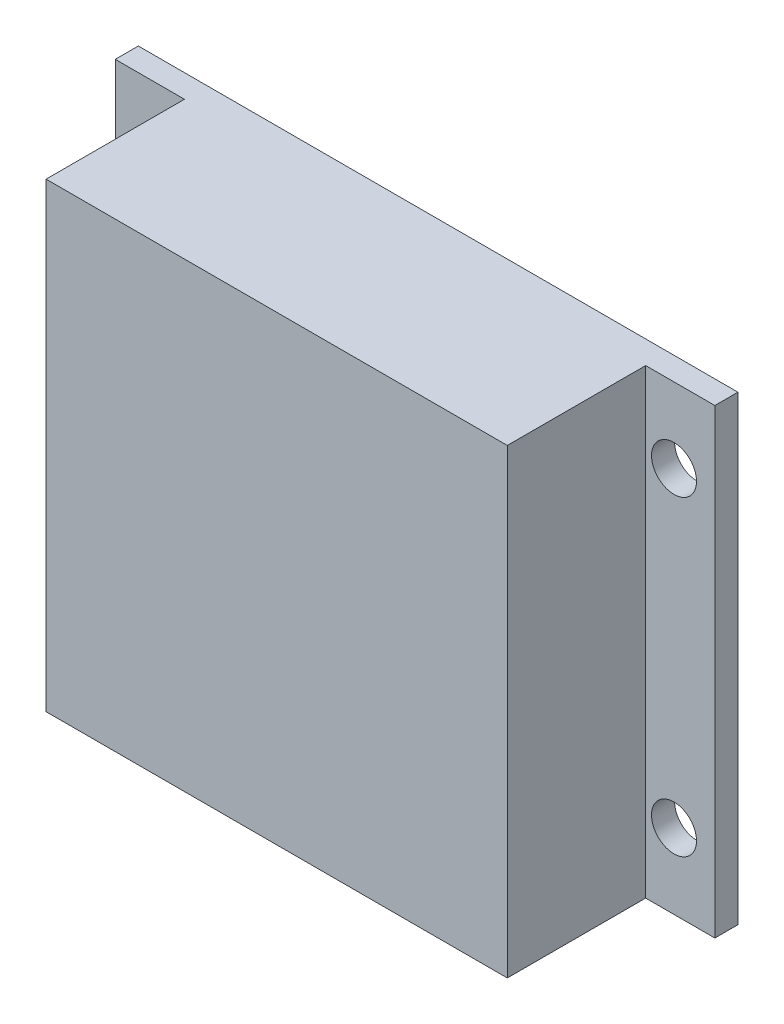
SolidWorks part; units mm, degrees
ref_plane "Front Plane" through (0, 0, 0) normal (0, 0, 1) x (1, 0, 0)
ref_plane "Top Plane" through (0, 0, 0) normal (0, 1, 0) x (1, 0, 0)
ref_plane "Right Plane" through (0, 0, 0) normal (1, 0, 0) x (0, 0, -1)
sketch "Sketch2" plane through (0, 0, 0) normal (0, 0, 1) x (1, 0, 0)
  line L1 (13, -10) -> (-13, -10)
  line L2 (13, -10) -> (13, 10)
  line L3 (13, 10) -> (-13, 10)
  line L4 (-13, -10) -> (-13, 10)
  line L5 (13, -10) -> (-13, 10) construction
  line L6 (13, 10) -> (-13, -10) construction
  line L7 (10, -10) -> (-10, -10)
  line L8 (10, -10) -> (10, 10)
  line L9 (10, 10) -> (-10, 10)
  line L10 (-10, -10) -> (-10, 10)
  line L11 (10, -10) -> (-10, 10) construction
  line L12 (10, 10) -> (-10, -10) construction
  point P0 (0, 0)
  point P6 (0, 0)
  point P7 (0, 0)
  dimension "D1" = 26
  dimension "D2" = 20
  dimension "D3" = 20
extrude "Boss-Extrude1" add sketch "Sketch2" along normal blind 1 contours L4 L3 L2 L1
sketch "Sketch3" plane through (0, 0, 1) normal (0, 0, 1) x (1, 0, 0)
  line L1 (10, -10) -> (-10, -10)
  line L2 (10, -10) -> (10, 10)
  line L3 (10, 10) -> (-10, 10)
  line L4 (-10, -10) -> (-10, 10)
  line L5 (10, -10) -> (-10, 10) construction
  line L6 (10, 10) -> (-10, -10) construction
  point P1 (0, 0)
  dimension "D1" = 20
  dimension "D2" = 20
extrude "Boss-Extrude2" add sketch "Sketch3" along normal blind 6
sketch "Sketch4" plane through (0, 0, 1) normal (0, 0, 1) x (1, 0, 0)
  line L0 (-13, -10) -> (-13, 10) construction
  line L1 (-10, 10) -> (-13, 10) construction
  circle A0 centre (-11.23, 6.75) radius 0.975
  dimension "D1" = 1.95
  dimension "D2" = 1.77
  dimension "D3" = 3.25
extrude "Cut-Extrude1" cut sketch "Sketch4" against normal through all contours A0
mirror "Mirror1" about plane through (0, 0, 0) normal (1, 0, 0) of "Cut-Extrude1"
mirror "Mirror2" about plane through (0, 0, 0) normal (0, 1, 0) of "Cut-Extrude1", "Mirror1"
